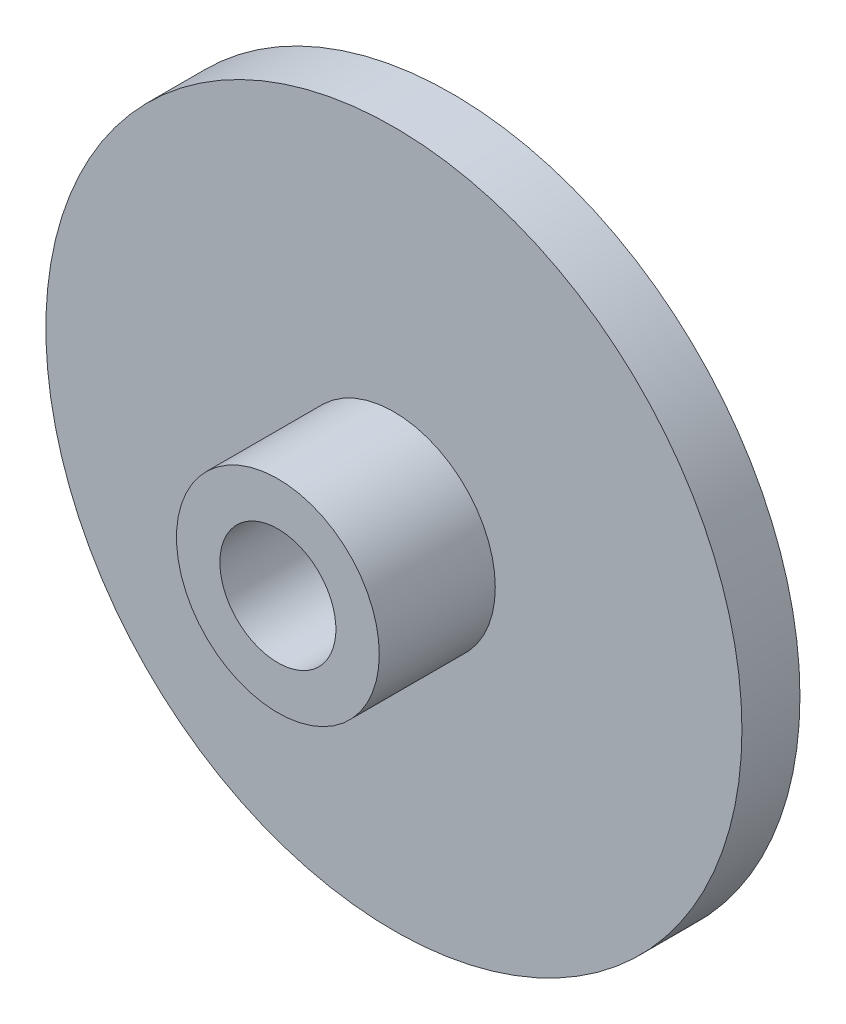
SolidWorks part; units mm, degrees
ref_plane "Front Plane" through (0, 0, 0) normal (0, 0, 1) x (1, 0, 0)
ref_plane "Top Plane" through (0, 0, 0) normal (0, 1, 0) x (1, 0, 0)
ref_plane "Right Plane" through (0, 0, 0) normal (1, 0, 0) x (0, 0, -1)
sketch "Sketch1" plane through (0, 0, 0) normal (0, 0, 1) x (1, 0, 0)
  circle A0 centre (0, 0) radius 19.05
extrude "Boss-Extrude1" add sketch "Sketch1" along normal blind 3.175
sketch "Sketch2" plane through (0, 0, 3.175) normal (0, 0, 1) x (1, 0, 0)
  circle A0 centre (0, 0) radius 5.5499
extrude "Boss-Extrude2" add sketch "Sketch2" along normal blind 6.35
sketch "Sketch3" plane through (0, 0, 0) normal (0, 0, -1) x (-1, 0, 0)
  circle A0 centre (0, 0) radius 3.175
extrude "Cut-Extrude1" cut sketch "Sketch3" against normal blind 9.525
